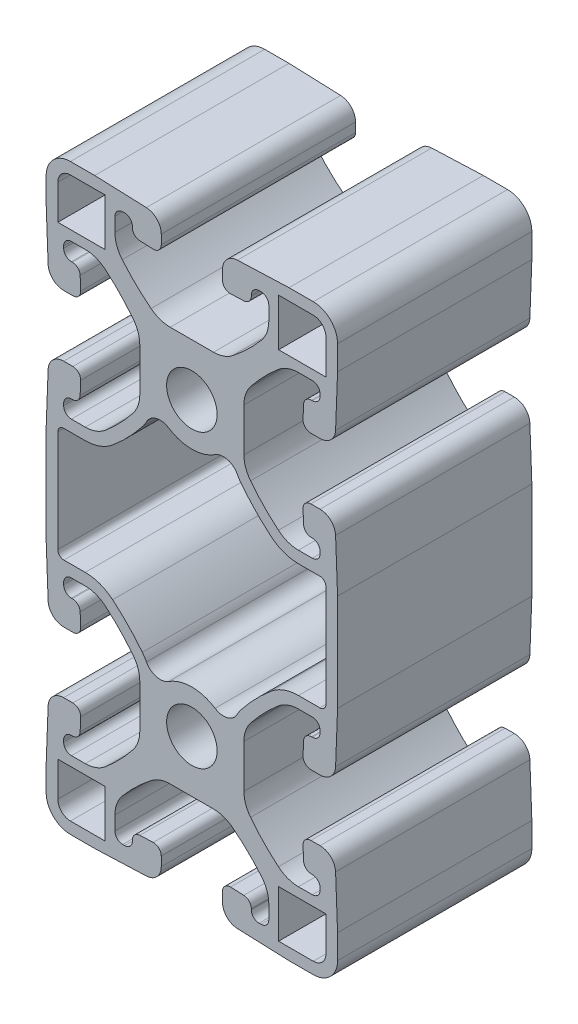
SolidWorks part; units mm, degrees
material "6061 Alloy"
ref_plane "Front" through (0, 0, 0) normal (0, 0, 1) x (1, 0, 0)
ref_plane "Top" through (0, 0, 0) normal (0, 1, 0) x (1, 0, 0)
ref_plane "Right" through (0, 0, 0) normal (1, 0, 0) x (0, 0, -1)
sketch "Sketch1" plane through (0, 0, 0) normal (0, 0, 1) x (1, 0, 0)
  line L0 (13.9468, 26.5049) -> (16.7322, 26.5049)
  line L1 (-16.7322, 26.5049) -> (-13.9468, 26.5049)
  line L2 (17.526, 25.7112) -> (17.526, 12.3888)
  line L3 (-17.526, 12.3888) -> (-17.526, 25.7112)
  line L4 (16.7322, 11.5951) -> (13.9468, 11.5951)
  line L5 (-13.9468, 11.5951) -> (-16.7322, 11.5951)
  line L6 (6.8072, 35.2719) -> (6.8072, 40.9281)
  line L7 (13.9316, 48.1584) -> (15.748, 48.1584)
  line L8 (15.748, 28.0416) -> (13.9316, 28.0416)
  line L9 (16.764, 47.1424) -> (16.764, 46.8884)
  line L10 (16.764, 29.3116) -> (16.764, 29.0576)
  line L11 (15.748, 45.8724) -> (15.6189, 45.8724)
  line L12 (15.6189, 30.3276) -> (15.748, 30.3276)
  line L13 (14.6037, 44.8954) -> (14.5368, 43.1555)
  line L14 (14.5368, 33.0445) -> (14.6037, 31.3046)
  line L15 (15.5521, 42.1005) -> (16.7604, 42.1005)
  line L16 (16.7604, 34.0995) -> (15.5521, 34.0995)
  line L17 (18.7909, 44.0545) -> (19.05, 50.8)
  line L18 (19.05, 25.4) -> (18.7909, 32.1455)
  line L19 (19.05, 50.8) -> (19.05, 53.975)
  line L20 (19.05, 12.7) -> (19.05, 25.4)
  line L21 (18.7909, 5.9545) -> (19.05, 12.7)
  line L22 (15.875, 57.15) -> (12.7, 57.15)
  line L23 (12.7, 57.15) -> (5.9545, 56.8909)
  line L24 (15.5521, 4.0005) -> (16.7604, 4.0005)
  line L25 (4.0005, 54.8604) -> (4.0005, 53.6521)
  line L26 (14.6037, 6.7954) -> (14.5368, 5.0555)
  line L27 (5.0555, 52.6368) -> (6.7954, 52.7037)
  line L28 (15.748, 7.7724) -> (15.6189, 7.7724)
  line L29 (7.7724, 53.7189) -> (7.7724, 53.848)
  line L30 (16.764, 9.0424) -> (16.764, 8.7884)
  line L31 (8.7884, 54.864) -> (9.0424, 54.864)
  line L32 (13.9316, 10.0584) -> (15.748, 10.0584)
  line L33 (10.0584, 53.848) -> (10.0584, 52.0316)
  line L34 (6.8072, -2.8281) -> (6.8072, 2.8281)
  line L35 (2.8281, 44.9072) -> (-2.8281, 44.9072)
  line L36 (15.748, -10.0584) -> (13.9316, -10.0584)
  line L37 (-10.0584, 52.0316) -> (-10.0584, 53.848)
  line L38 (16.764, -8.7884) -> (16.764, -9.0424)
  line L39 (-9.0424, 54.864) -> (-8.7884, 54.864)
  line L40 (15.6189, -7.7724) -> (15.748, -7.7724)
  line L41 (-7.7724, 53.848) -> (-7.7724, 53.7189)
  line L42 (14.5368, -5.0555) -> (14.6037, -6.7954)
  line L43 (-6.7954, 52.7037) -> (-5.0555, 52.6368)
  line L44 (16.7604, -4.0005) -> (15.5521, -4.0005)
  line L45 (-4.0005, 53.6521) -> (-4.0005, 54.8604)
  line L46 (19.05, -12.7) -> (18.7909, -5.9545)
  line L47 (19.05, -15.875) -> (19.05, -12.7)
  line L48 (-5.9545, 56.8909) -> (-12.7, 57.15)
  line L49 (-12.7, 57.15) -> (-15.875, 57.15)
  line L50 (12.7, -19.05) -> (15.875, -19.05)
  line L51 (5.9545, -18.7909) -> (12.7, -19.05)
  line L52 (-19.05, 53.975) -> (-19.05, 50.8)
  line L53 (-19.05, 50.8) -> (-18.7909, 44.0545)
  line L54 (4.0005, -15.5521) -> (4.0005, -16.7604)
  line L55 (-16.7604, 42.1005) -> (-15.5521, 42.1005)
  line L56 (6.7954, -14.6037) -> (5.0555, -14.5368)
  line L57 (-14.5368, 43.1555) -> (-14.6037, 44.8954)
  line L58 (7.7724, -15.748) -> (7.7724, -15.6189)
  line L59 (-15.6189, 45.8724) -> (-15.748, 45.8724)
  line L60 (9.0424, -16.764) -> (8.7884, -16.764)
  line L61 (-16.764, 46.8884) -> (-16.764, 47.1424)
  line L62 (10.0584, -13.9316) -> (10.0584, -15.748)
  line L63 (-15.748, 48.1584) -> (-13.9316, 48.1584)
  line L64 (-2.8281, -6.8072) -> (2.8281, -6.8072)
  line L65 (-6.8072, 40.9281) -> (-6.8072, 35.2719)
  line L66 (-10.0584, -15.748) -> (-10.0584, -13.9316)
  line L67 (-13.9316, 28.0416) -> (-15.748, 28.0416)
  line L68 (-8.7884, -16.764) -> (-9.0424, -16.764)
  line L69 (-16.764, 29.0576) -> (-16.764, 29.3116)
  line L70 (-7.7724, -15.6189) -> (-7.7724, -15.748)
  line L71 (-15.748, 30.3276) -> (-15.6189, 30.3276)
  line L72 (-5.0555, -14.5368) -> (-6.7954, -14.6037)
  line L73 (-14.6037, 31.3046) -> (-14.5368, 33.0445)
  line L74 (-4.0005, -16.7604) -> (-4.0005, -15.5521)
  line L75 (-15.5521, 34.0995) -> (-16.7604, 34.0995)
  line L76 (-12.7, -19.05) -> (-5.9545, -18.7909)
  line L77 (-15.875, -19.05) -> (-12.7, -19.05)
  line L78 (-18.7909, 32.1455) -> (-19.05, 25.4)
  line L79 (-19.05, 25.4) -> (-19.05, 12.7)
  line L80 (-19.05, -12.7) -> (-19.05, -15.875)
  line L81 (-19.05, 12.7) -> (-18.7909, 5.9545)
  line L82 (-18.7909, -5.9545) -> (-19.05, -12.7)
  line L83 (-16.7604, 4.0005) -> (-15.5521, 4.0005)
  line L84 (-15.5521, -4.0005) -> (-16.7604, -4.0005)
  line L85 (-14.5368, 5.0555) -> (-14.6037, 6.7954)
  line L86 (-14.6037, -6.7954) -> (-14.5368, -5.0555)
  line L87 (-15.6189, 7.7724) -> (-15.748, 7.7724)
  line L88 (-15.748, -7.7724) -> (-15.6189, -7.7724)
  line L89 (-16.764, 8.7884) -> (-16.764, 9.0424)
  line L90 (-16.764, -9.0424) -> (-16.764, -8.7884)
  line L91 (-15.748, 10.0584) -> (-13.9316, 10.0584)
  line L92 (-13.9316, -10.0584) -> (-15.748, -10.0584)
  line L93 (-6.8072, 2.8281) -> (-6.8072, -2.8281)
  line L94 (-11.3411, -17.526) -> (-15.875, -17.526)
  line L95 (-11.3411, -11.3411) -> (-11.3411, -17.526)
  line L96 (-17.526, -11.3411) -> (-11.3411, -11.3411)
  line L97 (-17.526, -15.875) -> (-17.526, -11.3411)
  line L98 (11.3411, -11.3411) -> (17.526, -11.3411)
  line L99 (11.3411, -17.526) -> (11.3411, -11.3411)
  line L100 (17.526, -11.3411) -> (17.526, -15.875)
  line L101 (15.875, -17.526) -> (11.3411, -17.526)
  line L102 (-17.526, 49.4411) -> (-17.526, 53.975)
  line L103 (-15.875, 55.626) -> (-11.3411, 55.626)
  line L104 (-11.3411, 49.4411) -> (-17.526, 49.4411)
  line L105 (-11.3411, 55.626) -> (-11.3411, 49.4411)
  line L106 (17.526, 53.975) -> (17.526, 49.4411)
  line L107 (17.526, 49.4411) -> (11.3411, 49.4411)
  line L108 (11.3411, 55.626) -> (15.875, 55.626)
  line L109 (11.3411, 49.4411) -> (11.3411, 55.626)
  arc A0 (5.9343, 32.6541) -> (3.0353, 33.4083) centre (4.1391, 31.7022) ccw
  arc A1 (-3.0353, 33.4083) -> (3.0353, 33.4083) centre (0, 38.1) ccw
  arc A2 (5.9343, 32.6541) -> (6.474, 31.8237) centre (10.8712, 35.2719) ccw
  arc A3 (-3.0353, 33.4083) -> (-5.9343, 32.6541) centre (-4.1391, 31.7022) ccw
  arc A4 (6.474, 31.8237) -> (10.3551, 27.8121) centre (27.6606, 48.4378) ccw
  arc A5 (-6.474, 31.8237) -> (-5.9343, 32.6541) centre (-10.8712, 35.2719) ccw
  arc A6 (10.3551, 27.8121) -> (13.9468, 26.5049) centre (13.9468, 32.0929) ccw
  arc A7 (-10.3551, 27.8121) -> (-6.474, 31.8237) centre (-27.6606, 48.4378) ccw
  arc A8 (-13.9468, 26.5049) -> (-10.3551, 27.8121) centre (-13.9468, 32.0929) ccw
  arc A9 (17.526, 25.7112) -> (16.7322, 26.5049) centre (16.7322, 25.7112) ccw
  arc A10 (-16.7322, 26.5049) -> (-17.526, 25.7112) centre (-16.7322, 25.7112) ccw
  arc A11 (16.7322, 11.5951) -> (17.526, 12.3888) centre (16.7322, 12.3888) ccw
  arc A12 (-17.526, 12.3888) -> (-16.7322, 11.5951) centre (-16.7322, 12.3888) ccw
  arc A13 (13.9468, 11.5951) -> (10.3551, 10.2879) centre (13.9468, 6.0071) ccw
  arc A14 (10.3551, 10.2879) -> (6.474, 6.2763) centre (27.6606, -10.3378) ccw
  arc A15 (-10.3551, 10.2879) -> (-13.9468, 11.5951) centre (-13.9468, 6.0071) ccw
  arc A16 (6.474, 6.2763) -> (5.9343, 5.4459) centre (10.8712, 2.8281) ccw
  arc A17 (-6.474, 6.2763) -> (-10.3551, 10.2879) centre (-27.6606, -10.3378) ccw
  arc A18 (3.0353, 4.6917) -> (5.9343, 5.4459) centre (4.1391, 6.3978) ccw
  arc A19 (-5.9343, 5.4459) -> (-6.474, 6.2763) centre (-10.8712, 2.8281) ccw
  arc A20 (3.0353, 4.6917) -> (-3.0353, 4.6917) centre (0, 0) ccw
  arc A21 (-5.9343, 5.4459) -> (-3.0353, 4.6917) centre (-4.1391, 6.3978) ccw
  arc A22 (7.6732, 43.4359) -> (6.8072, 40.9281) centre (10.8712, 40.9281) ccw
  arc A23 (6.8072, 35.2719) -> (7.6732, 32.7641) centre (10.8712, 35.2719) ccw
  arc A24 (11.3166, 47.2053) -> (7.6732, 43.4359) centre (27.6606, 27.7622) ccw
  arc A25 (7.6732, 32.7641) -> (11.3166, 28.9947) centre (27.6606, 48.4378) ccw
  arc A26 (13.9316, 48.1584) -> (11.3166, 47.2053) centre (13.9316, 44.0944) ccw
  arc A27 (11.3166, 28.9947) -> (13.9316, 28.0416) centre (13.9316, 32.1056) ccw
  arc A28 (16.764, 47.1424) -> (15.748, 48.1584) centre (15.748, 47.1424) ccw
  arc A29 (15.748, 28.0416) -> (16.764, 29.0576) centre (15.748, 29.0576) ccw
  arc A30 (15.748, 45.8724) -> (16.764, 46.8884) centre (15.748, 46.8884) ccw
  arc A31 (16.764, 29.3116) -> (15.748, 30.3276) centre (15.748, 29.3116) ccw
  arc A32 (15.6189, 45.8724) -> (14.6037, 44.8954) centre (15.6189, 44.8564) ccw
  arc A33 (14.6037, 31.3046) -> (15.6189, 30.3276) centre (15.6189, 31.3436) ccw
  arc A34 (14.5368, 43.1555) -> (15.5521, 42.1005) centre (15.5521, 43.1165) ccw
  arc A35 (15.5521, 34.0995) -> (14.5368, 33.0445) centre (15.5521, 33.0835) ccw
  arc A36 (16.7604, 42.1005) -> (18.7909, 44.0545) centre (16.7604, 44.1325) ccw
  arc A37 (18.7909, 32.1455) -> (16.7604, 34.0995) centre (16.7604, 32.0675) ccw
  arc A38 (19.05, 53.975) -> (15.875, 57.15) centre (15.875, 53.975) ccw
  arc A39 (16.7604, 4.0005) -> (18.7909, 5.9545) centre (16.7604, 6.0325) ccw
  arc A40 (5.9545, 56.8909) -> (4.0005, 54.8604) centre (6.0325, 54.8604) ccw
  arc A41 (14.5368, 5.0555) -> (15.5521, 4.0005) centre (15.5521, 5.0165) ccw
  arc A42 (4.0005, 53.6521) -> (5.0555, 52.6368) centre (5.0165, 53.6521) ccw
  arc A43 (15.6189, 7.7724) -> (14.6037, 6.7954) centre (15.6189, 6.7564) ccw
  arc A44 (6.7954, 52.7037) -> (7.7724, 53.7189) centre (6.7564, 53.7189) ccw
  arc A45 (15.748, 7.7724) -> (16.764, 8.7884) centre (15.748, 8.7884) ccw
  arc A46 (8.7884, 54.864) -> (7.7724, 53.848) centre (8.7884, 53.848) ccw
  arc A47 (16.764, 9.0424) -> (15.748, 10.0584) centre (15.748, 9.0424) ccw
  arc A48 (10.0584, 53.848) -> (9.0424, 54.864) centre (9.0424, 53.848) ccw
  arc A49 (13.9316, 10.0584) -> (11.3166, 9.1053) centre (13.9316, 5.9944) ccw
  arc A50 (11.3166, 9.1053) -> (7.6732, 5.3359) centre (27.6606, -10.3378) ccw
  arc A51 (9.1053, 49.4166) -> (10.0584, 52.0316) centre (5.9944, 52.0316) ccw
  arc A52 (7.6732, 5.3359) -> (6.8072, 2.8281) centre (10.8712, 2.8281) ccw
  arc A53 (5.3359, 45.7732) -> (9.1053, 49.4166) centre (-10.3378, 65.7606) ccw
  arc A54 (2.8281, 44.9072) -> (5.3359, 45.7732) centre (2.8281, 48.9712) ccw
  arc A55 (6.8072, -2.8281) -> (7.6732, -5.3359) centre (10.8712, -2.8281) ccw
  arc A56 (7.6732, -5.3359) -> (11.3166, -9.1053) centre (27.6606, 10.3378) ccw
  arc A57 (-5.3359, 45.7732) -> (-2.8281, 44.9072) centre (-2.8281, 48.9712) ccw
  arc A58 (11.3166, -9.1053) -> (13.9316, -10.0584) centre (13.9316, -5.9944) ccw
  arc A59 (-9.1053, 49.4166) -> (-5.3359, 45.7732) centre (10.3378, 65.7606) ccw
  arc A60 (-10.0584, 52.0316) -> (-9.1053, 49.4166) centre (-5.9944, 52.0316) ccw
  arc A61 (15.748, -10.0584) -> (16.764, -9.0424) centre (15.748, -9.0424) ccw
  arc A62 (-9.0424, 54.864) -> (-10.0584, 53.848) centre (-9.0424, 53.848) ccw
  arc A63 (16.764, -8.7884) -> (15.748, -7.7724) centre (15.748, -8.7884) ccw
  arc A64 (-7.7724, 53.848) -> (-8.7884, 54.864) centre (-8.7884, 53.848) ccw
  arc A65 (14.6037, -6.7954) -> (15.6189, -7.7724) centre (15.6189, -6.7564) ccw
  arc A66 (-7.7724, 53.7189) -> (-6.7954, 52.7037) centre (-6.7564, 53.7189) ccw
  arc A67 (15.5521, -4.0005) -> (14.5368, -5.0555) centre (15.5521, -5.0165) ccw
  arc A68 (-5.0555, 52.6368) -> (-4.0005, 53.6521) centre (-5.0165, 53.6521) ccw
  arc A69 (18.7909, -5.9545) -> (16.7604, -4.0005) centre (16.7604, -6.0325) ccw
  arc A70 (-4.0005, 54.8604) -> (-5.9545, 56.8909) centre (-6.0325, 54.8604) ccw
  arc A71 (15.875, -19.05) -> (19.05, -15.875) centre (15.875, -15.875) ccw
  arc A72 (-15.875, 57.15) -> (-19.05, 53.975) centre (-15.875, 53.975) ccw
  arc A73 (4.0005, -16.7604) -> (5.9545, -18.7909) centre (6.0325, -16.7604) ccw
  arc A74 (-18.7909, 44.0545) -> (-16.7604, 42.1005) centre (-16.7604, 44.1325) ccw
  arc A75 (5.0555, -14.5368) -> (4.0005, -15.5521) centre (5.0165, -15.5521) ccw
  arc A76 (-15.5521, 42.1005) -> (-14.5368, 43.1555) centre (-15.5521, 43.1165) ccw
  arc A77 (7.7724, -15.6189) -> (6.7954, -14.6037) centre (6.7564, -15.6189) ccw
  arc A78 (-14.6037, 44.8954) -> (-15.6189, 45.8724) centre (-15.6189, 44.8564) ccw
  arc A79 (7.7724, -15.748) -> (8.7884, -16.764) centre (8.7884, -15.748) ccw
  arc A80 (-16.764, 46.8884) -> (-15.748, 45.8724) centre (-15.748, 46.8884) ccw
  arc A81 (9.0424, -16.764) -> (10.0584, -15.748) centre (9.0424, -15.748) ccw
  arc A82 (-15.748, 48.1584) -> (-16.764, 47.1424) centre (-15.748, 47.1424) ccw
  arc A83 (10.0584, -13.9316) -> (9.1053, -11.3166) centre (5.9944, -13.9316) ccw
  arc A84 (9.1053, -11.3166) -> (5.3359, -7.6732) centre (-10.3378, -27.6606) ccw
  arc A85 (-11.3166, 47.2053) -> (-13.9316, 48.1584) centre (-13.9316, 44.0944) ccw
  arc A86 (5.3359, -7.6732) -> (2.8281, -6.8072) centre (2.8281, -10.8712) ccw
  arc A87 (-7.6732, 43.4359) -> (-11.3166, 47.2053) centre (-27.6606, 27.7622) ccw
  arc A88 (-6.8072, 40.9281) -> (-7.6732, 43.4359) centre (-10.8712, 40.9281) ccw
  arc A89 (-2.8281, -6.8072) -> (-5.3359, -7.6732) centre (-2.8281, -10.8712) ccw
  arc A90 (-5.3359, -7.6732) -> (-9.1053, -11.3166) centre (10.3378, -27.6606) ccw
  arc A91 (-7.6732, 32.7641) -> (-6.8072, 35.2719) centre (-10.8712, 35.2719) ccw
  arc A92 (-9.1053, -11.3166) -> (-10.0584, -13.9316) centre (-5.9944, -13.9316) ccw
  arc A93 (-11.3166, 28.9947) -> (-7.6732, 32.7641) centre (-27.6606, 48.4378) ccw
  arc A94 (-13.9316, 28.0416) -> (-11.3166, 28.9947) centre (-13.9316, 32.1056) ccw
  arc A95 (-10.0584, -15.748) -> (-9.0424, -16.764) centre (-9.0424, -15.748) ccw
  arc A96 (-16.764, 29.0576) -> (-15.748, 28.0416) centre (-15.748, 29.0576) ccw
  arc A97 (-8.7884, -16.764) -> (-7.7724, -15.748) centre (-8.7884, -15.748) ccw
  arc A98 (-15.748, 30.3276) -> (-16.764, 29.3116) centre (-15.748, 29.3116) ccw
  arc A99 (-6.7954, -14.6037) -> (-7.7724, -15.6189) centre (-6.7564, -15.6189) ccw
  arc A100 (-15.6189, 30.3276) -> (-14.6037, 31.3046) centre (-15.6189, 31.3436) ccw
  arc A101 (-4.0005, -15.5521) -> (-5.0555, -14.5368) centre (-5.0165, -15.5521) ccw
  arc A102 (-14.5368, 33.0445) -> (-15.5521, 34.0995) centre (-15.5521, 33.0835) ccw
  arc A103 (-5.9545, -18.7909) -> (-4.0005, -16.7604) centre (-6.0325, -16.7604) ccw
  arc A104 (-16.7604, 34.0995) -> (-18.7909, 32.1455) centre (-16.7604, 32.0675) ccw
  arc A105 (-19.05, -15.875) -> (-15.875, -19.05) centre (-15.875, -15.875) ccw
  arc A106 (-18.7909, 5.9545) -> (-16.7604, 4.0005) centre (-16.7604, 6.0325) ccw
  arc A107 (-16.7604, -4.0005) -> (-18.7909, -5.9545) centre (-16.7604, -6.0325) ccw
  arc A108 (-15.5521, 4.0005) -> (-14.5368, 5.0555) centre (-15.5521, 5.0165) ccw
  arc A109 (-14.5368, -5.0555) -> (-15.5521, -4.0005) centre (-15.5521, -5.0165) ccw
  arc A110 (-14.6037, 6.7954) -> (-15.6189, 7.7724) centre (-15.6189, 6.7564) ccw
  arc A111 (-15.6189, -7.7724) -> (-14.6037, -6.7954) centre (-15.6189, -6.7564) ccw
  arc A112 (-16.764, 8.7884) -> (-15.748, 7.7724) centre (-15.748, 8.7884) ccw
  arc A113 (-15.748, -7.7724) -> (-16.764, -8.7884) centre (-15.748, -8.7884) ccw
  arc A114 (-15.748, 10.0584) -> (-16.764, 9.0424) centre (-15.748, 9.0424) ccw
  arc A115 (-16.764, -9.0424) -> (-15.748, -10.0584) centre (-15.748, -9.0424) ccw
  arc A116 (-11.3166, 9.1053) -> (-13.9316, 10.0584) centre (-13.9316, 5.9944) ccw
  arc A117 (-13.9316, -10.0584) -> (-11.3166, -9.1053) centre (-13.9316, -5.9944) ccw
  arc A118 (-7.6732, 5.3359) -> (-11.3166, 9.1053) centre (-27.6606, -10.3378) ccw
  arc A119 (-11.3166, -9.1053) -> (-7.6732, -5.3359) centre (-27.6606, 10.3378) ccw
  arc A120 (-6.8072, 2.8281) -> (-7.6732, 5.3359) centre (-10.8712, 2.8281) ccw
  arc A121 (-7.6732, -5.3359) -> (-6.8072, -2.8281) centre (-10.8712, -2.8281) ccw
  arc A122 (-17.526, -15.875) -> (-15.875, -17.526) centre (-15.875, -15.875) ccw
  arc A123 (15.875, -17.526) -> (17.526, -15.875) centre (15.875, -15.875) ccw
  circle A124 centre (0, 0) radius 3.302
  arc A125 (-15.875, 55.626) -> (-17.526, 53.975) centre (-15.875, 53.975) ccw
  circle A126 centre (0, 38.1) radius 3.302
  arc A127 (17.526, 53.975) -> (15.875, 55.626) centre (15.875, 53.975) ccw
extrude "Extrude1" add sketch "Sketch1" along normal blind 25.4
